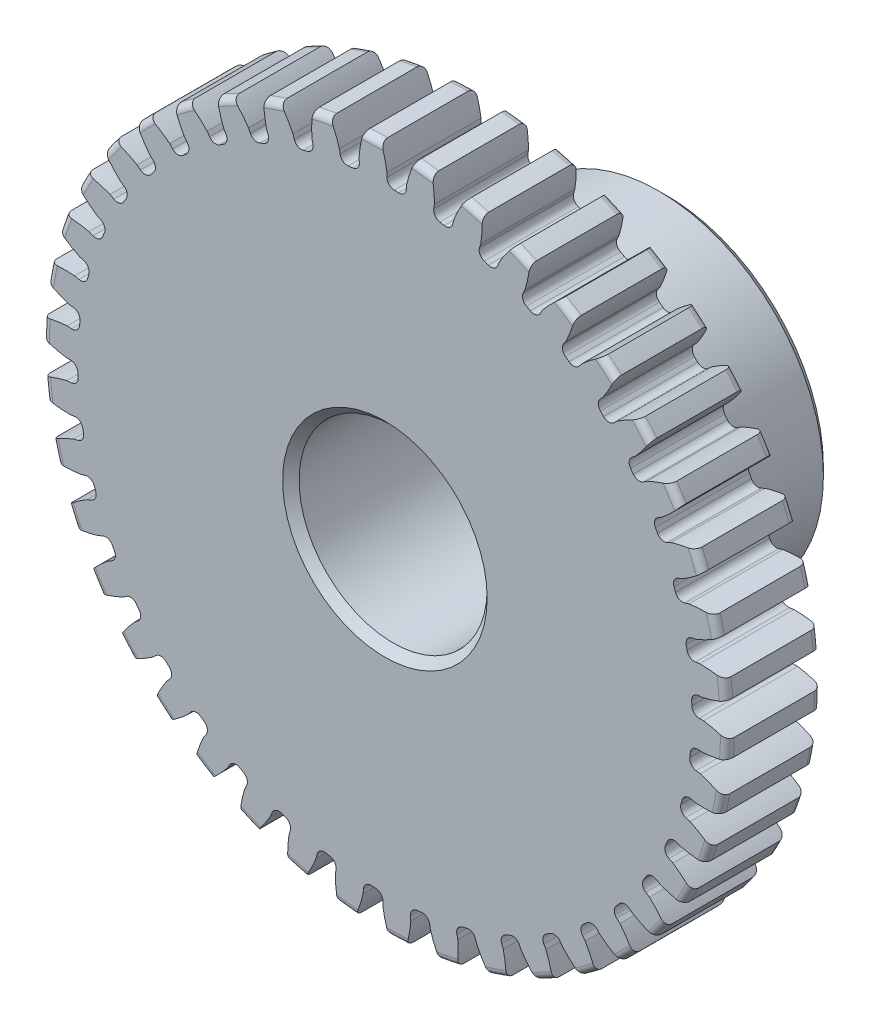
SolidWorks part; units mm, degrees
ref_plane "Front" through (0, 0, 0) normal (0, 0, 1) x (1, 0, 0)
ref_plane "Top" through (0, 0, 0) normal (0, 1, 0) x (1, 0, 0)
ref_plane "Right" through (0, 0, 0) normal (1, 0, 0) x (0, 0, -1)
sketch "Sketch1" plane through (0, 0, 0) normal (0, 0, 1) x (1, 0, 0)
  line L0 (-533.4, 0) -> (533.4, 0) construction
  circle A0 centre (0, 0) radius 11.557
  circle A1 centre (0, 0) radius 11.1125 construction
  circle A3 centre (0, 0) radius 10.3664 construction
  dimension "D3" = 0.4445
  dimension "D1" = 1.1906
extrude "Boss-Extrude1" add sketch "Sketch1" against normal blind 3.175
sketch "Sketch2" plane through (0, 0, 0) normal (1, 0, 0) x (0, 0, -1)
  line L0 (3.175, 0) -> (9.525, 0)
  line L1 (3.175, 0) -> (3.175, 5.5562)
  line L2 (3.175, 5.5562) -> (9.525, 5.5562)
  line L3 (9.525, 5.5562) -> (9.525, 0)
  point P5 (9.525, -5.5562)
  point P6 (0, -11.557)
  point P7 (3.175, -11.557)
  point P9 (0, 11.557)
revolve "Revolve1" add sketch "Sketch2" angle 360 mid plane about L0
fillet "Fillet2" radius 0.2311 3 edges at (11.557, 0, -3.175) (11.557, 0, 0) (5.5562, 0, -3.175)
sketch "Sketch3" plane through (0, 0, 0) normal (0, 0, 1) x (1, 0, 0)
  line L0 (0, 0) -> (0, 11.557) construction
  line L1 (-2.6937, 10.4159) -> (0, 11.1125)
  line L2 (-9.5921, 11.1125) -> (9.5921, 11.1125) construction
  line L3 (-9.2865, 8.7108) -> (9.2865, 13.5142) construction
  line L4 (-2.6937, 10.4159) -> (0, 0) construction
  line L5 (-6.8708, 8.2788) -> (0, 0) construction
  line L6 (-6.8708, 8.2788) -> (-1.1095, 13.0602) construction
  line L7 (-1.8783, 10.5933) -> (0, 0) construction
  line L8 (-1.8783, 10.5933) -> (0.0394, 10.9333) construction
  arc A0 (-2.6937, 10.4159) -> (-6.8708, 8.2788) centre (0, 0) ccw
  circle A1 centre (0, 0) radius 11.1125 construction
  circle A2 centre (0, 0) radius 10.7585 construction
  arc A3 (-2.6937, 10.4159) -> (-1.8783, 10.5933) centre (0, 0) cw
  circle A4 centre (0, 0) radius 11.557 construction
  point P6 (0, 11.1125)
  dimension "D1" = 2.7823
  dimension "D3" = 7.4869
  dimension "D5" = 1.9476
  dimension "D2" = 4.73
  dimension "D4" = 0.8347
sketch "Sketch4" plane through (0, 0, 0) normal (0, 0, 1) x (1, 0, 0)
  line L0 (0, 0) -> (0.4152, 11.097) construction
  line L1 (0.0698, 10.7583) -> (0.0698, 10.3661)
  line L2 (0, 11.1125) -> (0.8304, 11.0814) construction
  line L3 (0.7344, 10.7334) -> (0.7051, 10.3424)
  line L4 (0.0698, 10.3661) -> (0, 0) construction
  line L5 (0, 0) -> (0, 11.557) construction
  line L6 (-6.8708, 8.2788) -> (-1.1095, 13.0602) construction
  line L7 (-6.8708, 8.2788) -> (-1.1095, 13.0602) construction
  arc A0 (0.7051, 10.3424) -> (0.0698, 10.3661) centre (0, 0) ccw
  arc A1 (0, 11.1125) -> (0.8304, 11.0814) centre (0, 0) cw construction
  circle A2 centre (0, 0) radius 11.1125 construction
  circle A3 centre (0, 0) radius 10.7585 construction
  circle A4 centre (0, 0) radius 10.3664 construction
  arc A5 (2.0824, 12.9408) -> (-1.1095, 13.0602) centre (0, 0) ccw
  spline S0 degree 2 poles (-1.1095, 13.0602) (-0.1251, 12.0461) (0.0698, 10.7583) knots 0 0 0 1 1 1
  spline S1 degree 2 poles (2.0824, 12.9408) (1.025, 12.003) (0.7344, 10.7334) knots 0 0 0 1 1 1
  dimension "D1" = 0.8312
extrude "Cut-Extrude1" cut sketch "Sketch4" against normal through all
fillet "Fillet1" radius 0.2494 2 edges at (0.7051, 10.3424, -1.5875) (0.0698, 10.3661, -1.5875)
pattern_circular "CirPattern1" count 42 over 360 about axis through (0, 0, -3.175) along (0, 0, 1) of "Cut-Extrude1", "Fillet1"
sketch "Sketch5" plane through (0, 0, 0) normal (0, 0, 1) x (1, 0, 0)
  circle A0 centre (0, 0) radius 3.175
  circle A1 centre (0, 0) radius 1.5875 construction
  dimension "Bore Min" = 6.35
  dimension "Bore Max" = 3.175
extrude "Cut-Extrude2" cut sketch "Sketch5" against normal through all
chamfer "Chamfer1" distance 0.2778 angle 45 3 edges at (5.5562, 0, -9.525) (3.175, 0, 0) (3.175, 0, -9.525)
sketch "Pitch Dia" plane through (0, 0, 0) normal (0, 0, 1) x (1, 0, 0)
  circle A0 centre (0, 0) radius 11.1125 construction
  circle A1 centre (0, 0) radius 11.1125 construction
equation "\"D1@Boss-Extrude1\" = \"Face Wd@Sketch2\""
equation "\"D2@Sketch3\" = \"D1@Sketch3\"*1.7"
equation "\"D3@Sketch3\" = \"D1@Sketch3\"+\"D2@Sketch3\"-.001"
equation "\"D4@Sketch3\" = \"D1@Sketch3\"*.3"
equation "\"D5@Sketch3\" = \"D1@Sketch3\"-\"D4@Sketch3\""
equation "\"D1@Sketch4\" = 1.5708/(\"Number of Teeth@Sketch1\"/\"Ptich Dia@Sketch1\")"
equation "\"D1@Chamfer1\" = \"B Hub Dia@Sketch2\"*.025"
equation "\"D1@CirPattern1\" = \"Number of Teeth@Sketch1\""
equation "\"D1@Fillet1\" = \"D1@Sketch4\"*.3"
equation "\"D1@Fillet2\" = \"OD@Sketch1\"*.01"
equation "\"D1@Sketch1\" = 2.250/(\"Number of Teeth@Sketch1\"/\"Ptich Dia@Sketch1\")"
